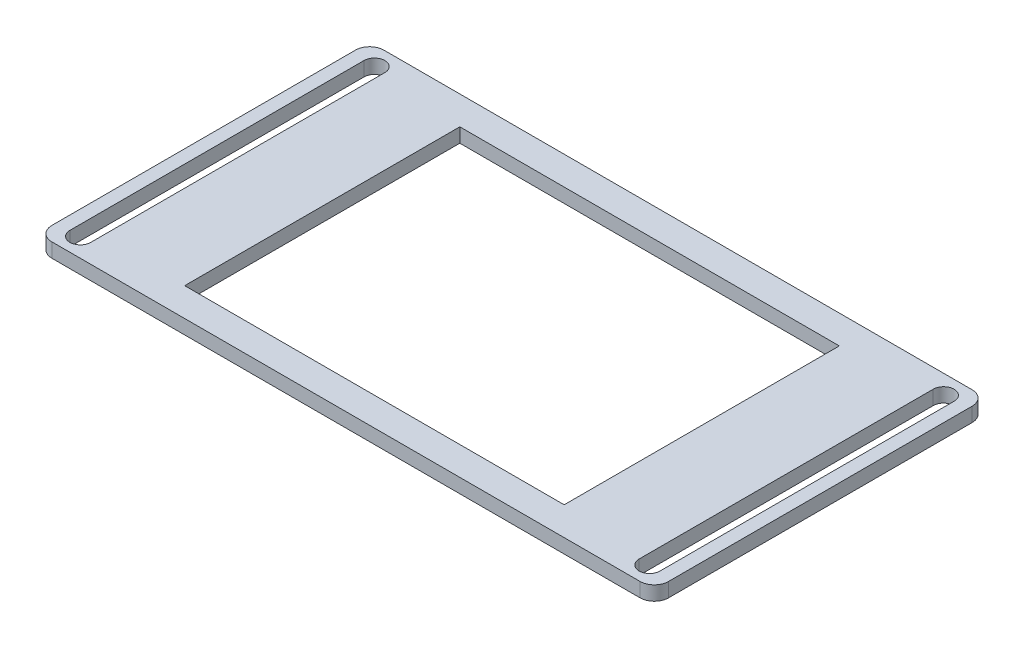
SolidWorks part; units mm, degrees
ref_plane "Front" through (0, 0, 0) normal (0, 0, 1) x (1, 0, 0)
ref_plane "Top" through (0, 0, 0) normal (0, 1, 0) x (1, 0, 0)
ref_plane "Right" through (0, 0, 0) normal (1, 0, 0) x (0, 0, -1)
sketch "Sketch1" plane through (0, 0, 0) normal (0, 1, 0) x (1, 0, 0)
  line L1 (-32.5, -17.5) -> (32.5, -17.5)
  line L2 (-32.5, -17.5) -> (-32.5, 17.5)
  line L3 (-32.5, 17.5) -> (32.5, 17.5)
  line L4 (32.5, -17.5) -> (32.5, 17.5)
  line L5 (-32.5, -17.5) -> (32.5, 17.5) construction
  line L6 (-32.5, 17.5) -> (32.5, -17.5) construction
  line L7 (-20, -14.5) -> (20, -14.5)
  line L8 (-20, -14.5) -> (-20, 14.5)
  line L9 (-20, 14.5) -> (20, 14.5)
  line L10 (20, -14.5) -> (20, 14.5)
  line L11 (-20, -14.5) -> (20, 14.5) construction
  line L12 (-20, 14.5) -> (20, -14.5) construction
  point P0 (0, 0)
  point P5 (0, 0)
  dimension "D1" = 35
  dimension "D2" = 65
  dimension "D3" = 40
  dimension "D4" = 3
extrude "Boss-Extrude1" add sketch "Sketch1" along normal blind 1.5
sketch "Sketch2" plane through (0, 1.5, 0) normal (0, 1, 0) x (1, 0, 0)
  line L0 (-30, -15.5) -> (-30, 15.5) construction
  line L1 (-31.1, -15.5) -> (-31.1, 15.5)
  line L2 (-28.9, -15.5) -> (-28.9, 15.5)
  line L3 (0, 0) -> (-30, 0) construction
  line L4 (0, 0) -> (0, 17.5) construction
  line L5 (32.5, 17.5) -> (-32.5, 17.5) construction
  line L6 (30, -15.5) -> (30, 15.5) construction
  line L7 (31.1, -15.5) -> (31.1, 15.5)
  line L8 (28.9, -15.5) -> (28.9, 15.5)
  line L9 (-32.5, -17.5) -> (32.5, -17.5) construction
  arc A0 (-31.1, -15.5) -> (-28.9, -15.5) centre (-30, -15.5) ccw
  arc A1 (-28.9, 15.5) -> (-31.1, 15.5) centre (-30, 15.5) ccw
  arc A2 (31.1, -15.5) -> (28.9, -15.5) centre (30, -15.5) cw
  arc A3 (28.9, 15.5) -> (31.1, 15.5) centre (30, 15.5) cw
  point P2 (-30, 0)
  point P15 (30, 0)
  dimension "D3" = 2.2
  dimension "D1" = 60
  dimension "D2" = 2
extrude "Cut-Extrude1" cut sketch "Sketch2" against normal through all
fillet "Fillet2" radius 1.5 4 edges at (-32.5, 0.75, -17.5) (32.5, 0.75, -17.5) (32.5, 0.75, 17.5) (-32.5, 0.75, 17.5)
